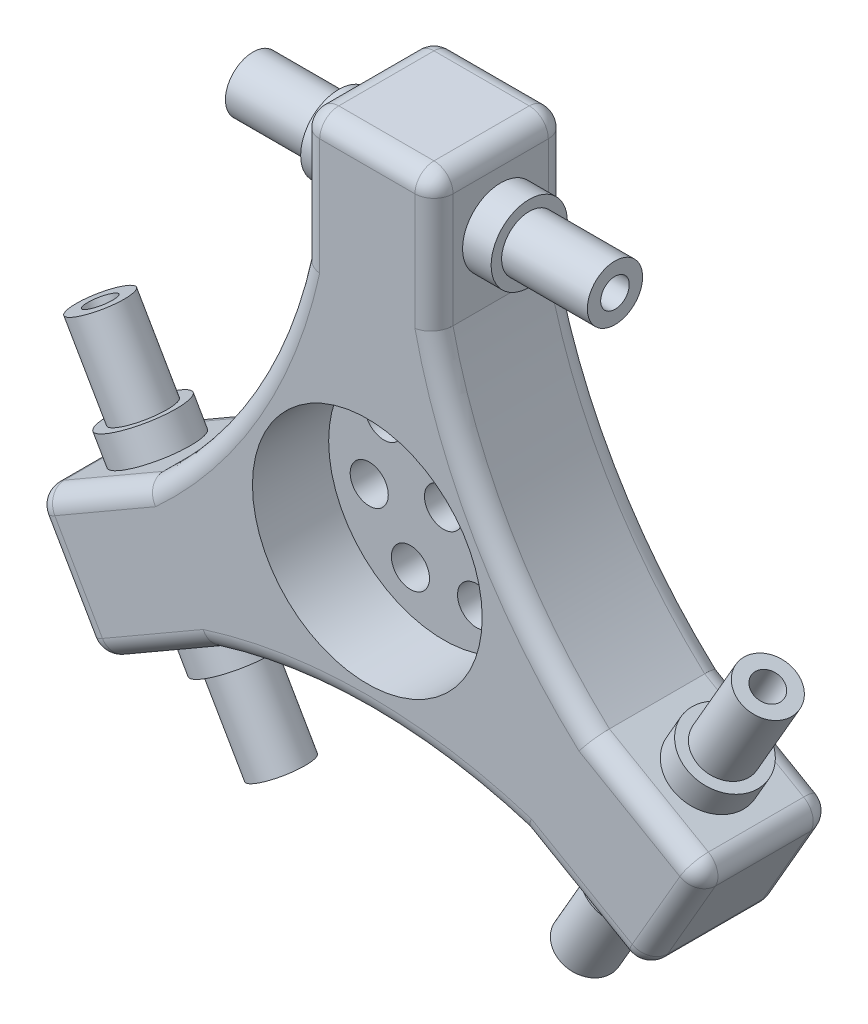
SolidWorks part; units mm, degrees
ref_plane "Front Plane" through (0, 0, 0) normal (0, 0, 1) x (1, 0, 0)
ref_plane "Top Plane" through (0, 0, 0) normal (0, 1, 0) x (1, 0, 0)
ref_plane "Right Plane" through (0, 0, 0) normal (1, 0, 0) x (0, 0, -1)
sketch "Sketch2" plane through (0, 0, 0) normal (0, 0, 1) x (1, 0, 0)
  line L0 (-7, 23) -> (-7, 37)
  line L1 (-7, 37) -> (7, 37)
  line L2 (7, 37) -> (7, 23)
  line L3 (23.4186, -5.4378) -> (35.5429, -12.4378)
  line L4 (35.5429, -12.4378) -> (28.5429, -24.5622)
  line L5 (28.5429, -24.5622) -> (16.4186, -17.5622)
  line L6 (-16.4186, -17.5622) -> (-28.5429, -24.5622)
  line L7 (-28.5429, -24.5622) -> (-35.5429, -12.4378)
  line L8 (-35.5429, -12.4378) -> (-23.4186, -5.4378)
  circle A3 centre (0, 0) radius 2
  arc A4 (7, 23) -> (23.4186, -5.4378) centre (60.6689, 35.0272) ccw
  arc A5 (16.4186, -17.5622) -> (-16.4186, -17.5622) centre (0, -70.0544) ccw
  arc A6 (-23.4186, -5.4378) -> (-7, 23) centre (-60.6689, 35.0272) ccw
  point P9 (0, 37)
  dimension "D1" = 55
  dimension "D5" = 4
  dimension "D2" = 14
  dimension "D6" = 14
  dimension "D7" = 14
  dimension "D4" = 3
  dimension "D8" = 3
extrude "Boss-Extrude1" add sketch "Sketch2" along normal blind 14
sketch "Sketch7" plane through (0, 0, 14) normal (0, 0, 1) x (1, 0, 0)
  circle A0 centre (0, 0) radius 12.0607
extrude "Cut-Extrude4" cut sketch "Sketch7" against normal blind 8
sketch "Sketch8" plane through (0, 0, 6) normal (0, 0, 1) x (1, 0, 0)
  circle A0 centre (0, 8) radius 2
  circle A1 centre (6.2547, 4.9879) radius 2
  circle A2 centre (7.7994, -1.7802) radius 2
  circle A3 centre (3.4711, -7.2078) radius 2
  circle A4 centre (-3.4711, -7.2078) radius 2
  circle A5 centre (-7.7994, -1.7802) radius 2
  circle A6 centre (-6.2547, 4.9879) radius 2
  dimension "D1" = 8
  dimension "D2" = 7
extrude "Cut-Extrude5" cut sketch "Sketch8" against normal blind 8
fillet "Fillet2" radius 2 6 edges at (0, 37, 0) (0, 37, 14) (-32.0429, -18.5, 0) (-32.0429, -18.5, 14) (32.0429, -18.5, 0) (32.0429, -18.5, 14)
sketch "Sketch10" plane through (3.5, 6.0622, 0) normal (0.5, 0.866, 0) x (0.866, -0.5, 0)
  line L0 (37, -12) -> (37, -2) construction
  line L1 (35, -14) -> (23, -14) construction
  circle A0 centre (29.5, -7) radius 4
  dimension "D1" = 8
  dimension "D2" = 7.5
  dimension "D3" = 7
fillet "Fillet4" radius 2 36 edges at (-35.0356, -12.1449, 0.5858) (-35.5429, -12.4378, 7) (-35.0356, -12.1449, 13.4142) (-7, 36.4142, 0.5858) (-7, 37, 7) (-7, 36.4142, 13.4142) (-28.0356, -24.2693, 13.4142) (-28.5429, -24.5622, 7) (-28.0356, -24.2693, 0.5858) (28.0356, -24.2693, 0.5858) (28.5429, -24.5622, 7) (28.0356, -24.2693, 13.4142) (7, 36.4142, 0.5858) (7, 37, 7) (7, 36.4142, 13.4142) (35.0356, -12.1449, 0.5858) (35.5429, -12.4378, 7) (35.0356, -12.1449, 13.4142) (28.6147, -8.4378, 0) (-7, 29, 0) (-13.0375, 7.5272, 0) (-28.6147, -8.4378, 0) (-28.6147, -8.4378, 14) (-13.0375, 7.5272, 14) (-7, 29, 14) (-21.6147, -20.5622, 14) (-21.6147, -20.5622, 0) (21.6147, -20.5622, 0) (21.6147, -20.5622, 14) (7, 29, 0) (13.0375, 7.5272, 0) (0, -15.0544, 0) (0, -15.0544, 14) (7, 29, 14) (28.6147, -8.4378, 14) (13.0375, 7.5272, 14)
extrude "Boss-Extrude3" add sketch "Sketch10" along normal blind 3
sketch "Sketch12" plane through (-3.5, -6.0622, 0) normal (-0.5, -0.866, 0) x (0.866, -0.5, 0)
  line L4 (23, 12) -> (23, 2)
  line L5 (23, 2) -> (35, 2)
  line L6 (35, 2) -> (35, 12)
  line L7 (35, 12) -> (23, 12)
  line L8 (23, 12) -> (23, 2)
  line L9 (23, 2) -> (35, 2)
  line L10 (35, 2) -> (35, 12)
  line L11 (35, 12) -> (23, 12)
  circle A1 centre (29.5, 7) radius 4
  circle A2 centre (29.5, 7) radius 4
  dimension "D1" = 0
  dimension "D2" = 0
sketch "Sketch13" plane through (-3.5, -6.0622, 0) normal (-0.5, -0.866, 0) x (0.866, -0.5, 0)
  circle A0 centre (29.5, 7) radius 4.0009
extrude "Boss-Extrude4" add sketch "Sketch13" along normal blind 3
sketch "Sketch15" plane through (5, 8.6603, 0) normal (0.5, 0.866, 0) x (0.866, -0.5, 0)
  circle A0 centre (29.5, -7) radius 2.9
  circle A1 centre (29.5, -7) radius 1.5
  dimension "D1" = 3
  dimension "D2" = 5.8
extrude "Boss-Extrude5" add sketch "Sketch15" along normal blind 9
sketch "Sketch16" plane through (-5, -8.6603, 0) normal (-0.5, -0.866, 0) x (0.866, -0.5, 0)
  circle A0 centre (29.5, 7) radius 2.9
  circle A1 centre (29.5, 7) radius 1.5
  dimension "D1" = 5.8
  dimension "D2" = 3
extrude "Boss-Extrude6" add sketch "Sketch16" along normal blind 9
pattern_circular "CirPattern1" count 3 over 360 about axis through (0, 0, 0) along (0, 0, 1) of "Boss-Extrude4", "Boss-Extrude5", "Boss-Extrude6", "Boss-Extrude3"
